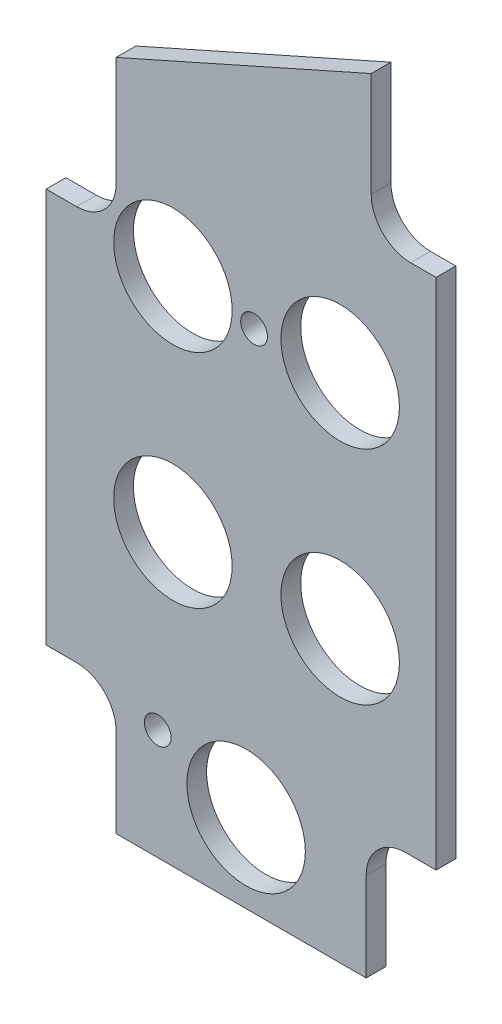
SolidWorks part; units mm, degrees
other "Camera1"
material "PET"
ref_plane "Front Plane" through (0, 0, 0) normal (0, 0, 1) x (1, 0, 0)
ref_plane "Top Plane" through (0, 0, 0) normal (0, 1, 0) x (1, 0, 0)
ref_plane "Right Plane" through (0, 0, 0) normal (1, 0, 0) x (0, 0, -1)
sketch "Sketch1" plane through (0, 0, 0) normal (0, 0, 1) x (1, 0, 0)
  line L8 (0, 103.0909) -> (0, 0)
  line L9 (0, 0) -> (62.6888, 0)
  line L10 (62.6888, 0) -> (62.6888, 131)
  line L11 (62.6888, 131) -> (0, 103.0909)
  dimension "D1" = 131
extrude "Boss-Extrude1" add sketch "Sketch1" against normal blind 3.175
sketch "Sketch2" plane through (0, 0, 0) normal (0, 0, 1) x (1, 0, 0)
  line L0 (0, 0) -> (62.6888, 0) construction
  line L1 (20.3732, 91.7104) -> (20.3732, 82.1854) construction
  line L2 (20.3732, 56.073) -> (20.3732, 46.548) construction
  line L3 (47.2705, 46.548) -> (47.2705, 56.073) construction
  line L4 (32.1439, 22.225) -> (32.1439, 12.7) construction
  line L5 (81.6444, 22.225) -> (81.6444, 12.7) construction
  line L6 (47.2705, 82.1854) -> (47.2705, 91.7104) construction
  line L7 (0, 103.0909) -> (0, 0) construction
  circle A4 centre (32.1439, 12.7) radius 9.525
  circle A10 centre (47.2705, 46.548) radius 9.525
  circle A12 centre (47.2705, 82.1854) radius 9.525
  circle A15 centre (20.3732, 82.1854) radius 9.525
  circle A17 centre (20.3732, 46.548) radius 9.525
  circle A18 centre (81.6444, 22.225) radius 1.651 construction
  circle A19 centre (81.6444, 12.7) radius 9.525 construction
  dimension "D2" = 12.7
  dimension "D3" = 19.05
  dimension "D5" = 19.05
  dimension ".75" = 19.05
  dimension "D1" = 9.525
  dimension "D4" = 32.1439
extrude "Cut-Extrude1" cut sketch "Sketch2" against normal through all
hole_wizard "#6 Clearance Hole1" positions "Sketch4" profile "Sketch3" hole size "#6" standard "ANSI Inch" end condition through all
sketch "Sketch4" plane through (0, 0, 0) normal (0, 0, 1) x (1, 0, 0)
  point P0 (58.6105, 14.2875)
  point P3 (4.8895, 14.2875)
  point P6 (4.8895, 90.4875)
  point P9 (58.6105, 109.5375)
sketch "Sketch3" plane through (58.6105, 14.2875, 0) normal (1, 0, 0) x (0, -1, 0)
  line L0 (0, 0) -> (0, 3.175)
  line L1 (0, 3.175) -> (2.1526, 3.175)
  line L2 (2.1526, 3.175) -> (2.1526, 0)
  line L5 (2.1526, 0) -> (0, 0)
  line L11 (0, -6.35) -> (0, 107.95) construction
  dimension "Thru Hole Dia." = 4.3053
  dimension "Thru Hole Depth" = 3.175
sketch "Sketch5" plane through (0, 0, 0) normal (0, 0, 1) x (1, 0, 0)
  line L0 (0, 0) -> (11.24, 0)
  line L1 (0, 0) -> (62.6888, 0) construction
  line L2 (0, 0) -> (0, 20.64)
  line L3 (0, 103.0909) -> (0, 0) construction
  line L4 (0, 20.64) -> (4.89, 20.64)
  line L5 (11.24, 14.29) -> (11.24, 0)
  line L6 (31.3444, 0) -> (31.3444, 117.0455) construction
  line L7 (62.6888, 131) -> (0, 103.0909) construction
  line L8 (51.4488, 14.29) -> (51.4488, 0)
  line L9 (62.6888, 20.64) -> (57.7988, 20.64)
  line L10 (62.6888, 0) -> (62.6888, 20.64)
  line L11 (62.6888, 0) -> (51.4488, 0)
  line L12 (0, 103.0909) -> (0, 84.1375)
  line L13 (0, 84.1375) -> (4.8895, 84.1375)
  line L14 (11.2395, 90.4875) -> (11.2395, 108.0948)
  line L15 (11.2395, 108.0948) -> (0, 103.0909)
  line L16 (62.6888, 131) -> (62.6888, 103.1875)
  line L17 (62.6888, 0) -> (62.6888, 131) construction
  line L18 (62.6888, 103.1875) -> (58.6105, 103.1875)
  line L19 (52.2605, 109.5375) -> (52.2605, 126.3573)
  line L20 (52.2605, 126.3573) -> (62.6888, 131)
  arc A0 (4.89, 20.64) -> (11.24, 14.29) centre (4.89, 14.29) cw
  arc A1 (57.7988, 20.64) -> (51.4488, 14.29) centre (57.7988, 14.29) ccw
  arc A2 (58.6105, 103.1875) -> (52.2605, 109.5375) centre (58.6105, 109.5375) cw
  arc A3 (4.8895, 84.1375) -> (11.2395, 90.4875) centre (4.8895, 90.4875) ccw
  point P37 (58.6105, 109.5375)
  dimension "D3" = 6.35
  dimension "D6" = 6.35
  dimension "D1" = 11.24
  dimension "D2" = 20.64
extrude "Cut-Extrude2" cut sketch "Sketch5" against normal through all
hole_wizard "#6 Clearance Hole2" positions "Sketch6" profile "Sketch7" hole size "#6" standard "ANSI Inch" end condition through all
sketch "Sketch6" plane through (31.75, 0, 3.175) normal (0, 0, 1) x (1, 0, 0)
  point P0 (1.6763, 81.3834)
  point P2 (-13.8187, 17.7712)
  point P3 (2.5973, 88.3171)
  point P4 (1.6763, 81.3834)
sketch "Sketch7" plane through (33.4263, 81.3834, 3.175) normal (1, 0, 0) x (0, -1, 0)
  line L0 (0, 0) -> (0, 6.35)
  line L1 (0, 6.35) -> (2.1526, 6.35)
  line L2 (2.1526, 6.35) -> (2.1526, 0)
  line L3 (2.1526, 0) -> (0, 0)
  line L4 (0, -6.35) -> (0, 107.95) construction
  dimension "Thru Hole Dia." = 4.3053
  dimension "Thru Hole Depth" = 6.35
